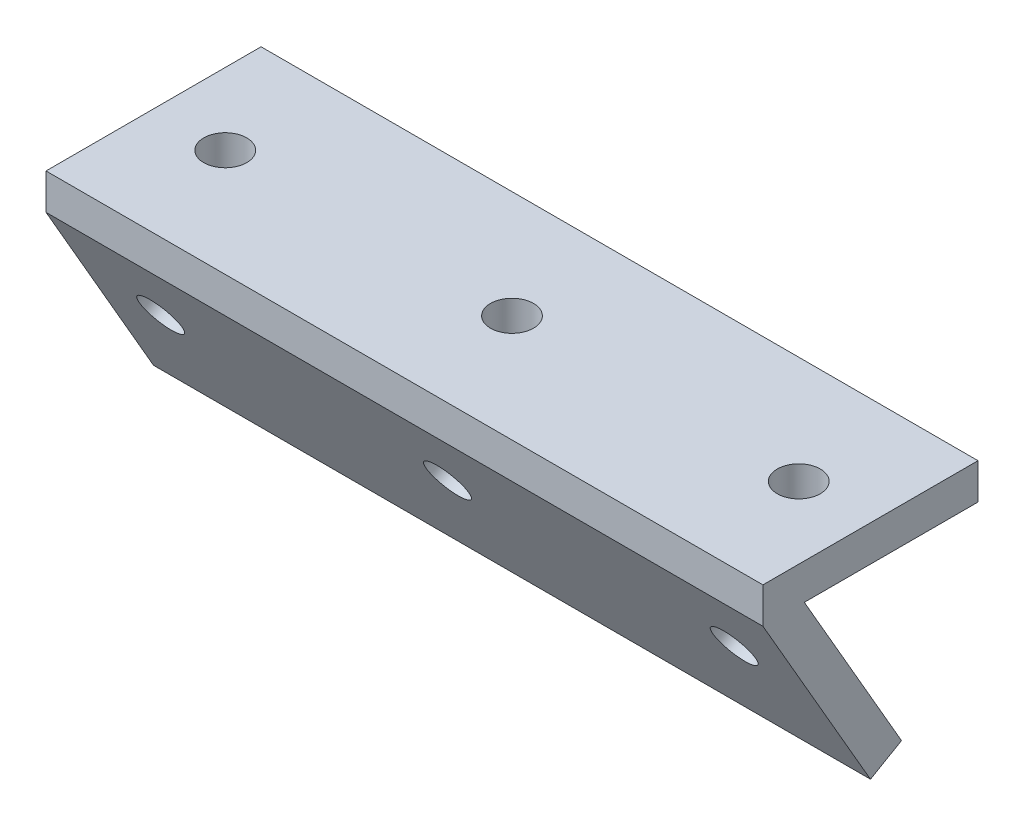
SolidWorks part; units mm, degrees
material "ABS"
ref_plane "Front Plane" through (0, 0, 0) normal (0, 0, 1) x (1, 0, 0)
ref_plane "Top Plane" through (0, 0, 0) normal (0, 1, 0) x (1, 0, 0)
ref_plane "Right Plane" through (0, 0, 0) normal (1, 0, 0) x (0, 0, -1)
sketch "Sketch2" plane through (0, 0, 0) normal (0, 1, 0) x (1, 0, 0)
  line L1 (-50, -15) -> (50, -15)
  line L2 (-50, -15) -> (-50, 15)
  line L3 (-50, 15) -> (50, 15)
  line L4 (50, -15) -> (50, 15)
  line L5 (-50, -15) -> (50, 15) construction
  line L6 (-50, 15) -> (50, -15) construction
  point P0 (0, 0)
  dimension "D1" = 30
  dimension "D2" = 100
extrude "Boss-Extrude1" add sketch "Sketch2" along normal blind 5 and the other way blind 0.0001 contours L1 L4 L3 L2
pattern_circular "CirPattern1" count 2 every 60 about axis through (0, -0.0001, 15) along (1, 0, 0) of "Boss-Extrude1"
sketch "Sketch4" plane through (0, -0.0001, 0) normal (0, -1, 0) x (1, 0, 0)
  line L0 (53.2147, 0) -> (-46.6871, 0) construction
  line L3 (50, 15) -> (50, -15) construction
  line L4 (-50, 15) -> (-50, -15) construction
  circle A0 centre (0, 0) radius 3
  circle A1 centre (40, 0) radius 3
  circle A2 centre (-40, 0) radius 3
  dimension "D1" = 6
  dimension "D2" = 10
  dimension "D3" = 10
extrude "Cut-Extrude1" cut sketch "Sketch4" against normal blind 10
sketch "Sketch5" plane through (0, -6.4952, 11.25) normal (0, -0.5, 0.866) x (1, 0, 0)
  line L0 (40, -4.5001) -> (-40, -4.5001) construction
  line L1 (50, 7.4999) -> (50, -22.5001) construction
  line L2 (-50, 7.4999) -> (-50, -22.5001) construction
  line L3 (-50, -22.5001) -> (50, -22.5001) construction
  circle A0 centre (40, -4.5001) radius 3
  circle A1 centre (0, -4.5001) radius 3
  circle A2 centre (-40, -4.5001) radius 3
  dimension "D1" = 6
  dimension "D2" = 10
  dimension "D3" = 10
  dimension "D4" = 18
extrude "Cut-Extrude2" cut sketch "Sketch5" against normal blind 10
